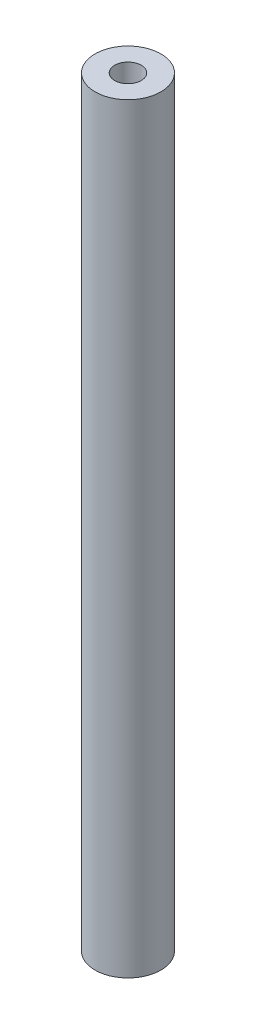
SolidWorks part; units mm, degrees
material "AISI 316 Annealed Stainless Steel Bar (SS)"
ref_plane "Front Plane" through (0, 0, 0) normal (0, 0, 1) x (1, 0, 0)
ref_plane "Top Plane" through (0, 0, 0) normal (0, 1, 0) x (1, 0, 0)
ref_plane "Right Plane" through (0, 0, 0) normal (1, 0, 0) x (0, 0, -1)
sketch "Sketch1" plane through (0, 0, 0) normal (0, 1, 0) x (1, 0, 0)
  circle A0 centre (0, 0) radius 5
  dimension "D1" = 10
extrude "Boss-Extrude2" add sketch "Sketch1" against normal blind 115.57
ref_plane "Plane1" through (0, 0, -5) normal (0, 0, -1) x (-1, 0, 0)
sketch "Sketch2" plane through (0, 0, -5) normal (0, 0, -1) x (-1, 0, 0)
  line L0 (0, -10.39) -> (0, -15.39) construction
  line L1 (0, -115.57) -> (0, 0) construction
  line L2 (1.5, -10.39) -> (1.5, -15.39)
  line L3 (-1.5, -10.39) -> (-1.5, -15.39)
  line L5 (0, -63.5) -> (0, -68.5) construction
  line L6 (1.5, -63.5) -> (1.5, -68.5)
  line L7 (-1.5, -63.5) -> (-1.5, -68.5)
  line L8 (5, 0) -> (-5, 0) construction
  line L9 (0, -109.22) -> (0, -114.22) construction
  line L10 (2, -109.22) -> (2, -114.22)
  line L11 (-2, -109.22) -> (-2, -114.22)
  arc A0 (1.5, -10.39) -> (-1.5, -10.39) centre (0, -10.39) ccw
  arc A1 (-1.5, -15.39) -> (1.5, -15.39) centre (0, -15.39) ccw
  arc A2 (1.5, -63.5) -> (-1.5, -63.5) centre (0, -63.5) ccw
  arc A3 (-1.5, -68.5) -> (1.5, -68.5) centre (0, -68.5) ccw
  arc A4 (2, -109.22) -> (-2, -109.22) centre (0, -109.22) ccw
  arc A5 (-2, -114.22) -> (2, -114.22) centre (0, -114.22) ccw
  point P5 (0, -12.89)
  point P10 (0, -8.89)
  point P11 (0, -16.89)
  point P14 (0, -66)
  point P19 (0, -111.72)
  dimension "D2" = 8
  dimension "D5" = 109.22
  dimension "D1" = 3
  dimension "D3" = 8.89
  dimension "D4" = 63.5
  dimension "D6" = 4
extrude "Cut-Extrude1" cut sketch "Sketch2" against normal blind 2.54 contours L11 A5 L10 A4 | L7 A3 L6 A2 | L3 A1 L2 A0
hole_wizard "Tap Drill for #10-32 Tap1" positions "3DSketch1" profile "Sketch3" hole size "#10-32" standard "ANSI Inch"
sketch3d "3DSketch1"
  line L0 (0, -115.57, 0) -> (0, 0, 0) construction
  circle A0 centre (0, 0, 0) radius 5 construction
  point P0 (0, 0, 0)
  point P3 (0, -115.57, 0)
  point P7 (0, 0, 0)
  point P9 (0, 0, 0)
  point P10 (0.706, 0, 0.4764)
  point P11 (0, 0, 0)
  point P14 (0, 5, 0)
sketch "Sketch3" plane through (0, 0, 0) normal (1, 0, 0) x (0, 0, 1)
  line L0 (0, 0) -> (0, 12.7)
  line L1 (0, 12.7) -> (2.0193, 11.4867)
  line L2 (2.0193, 11.4867) -> (2.0193, 0)
  line L5 (2.0193, 0) -> (0, 0)
  line L10 (0, 12.7) -> (-2.0193, 11.4867) construction
  line L11 (0, -6.35) -> (0, 107.95) construction
  dimension "Hole Dia." = 4.0386
  dimension "Hole Depth" = 12.7
  dimension "Drill Angle" = 118
